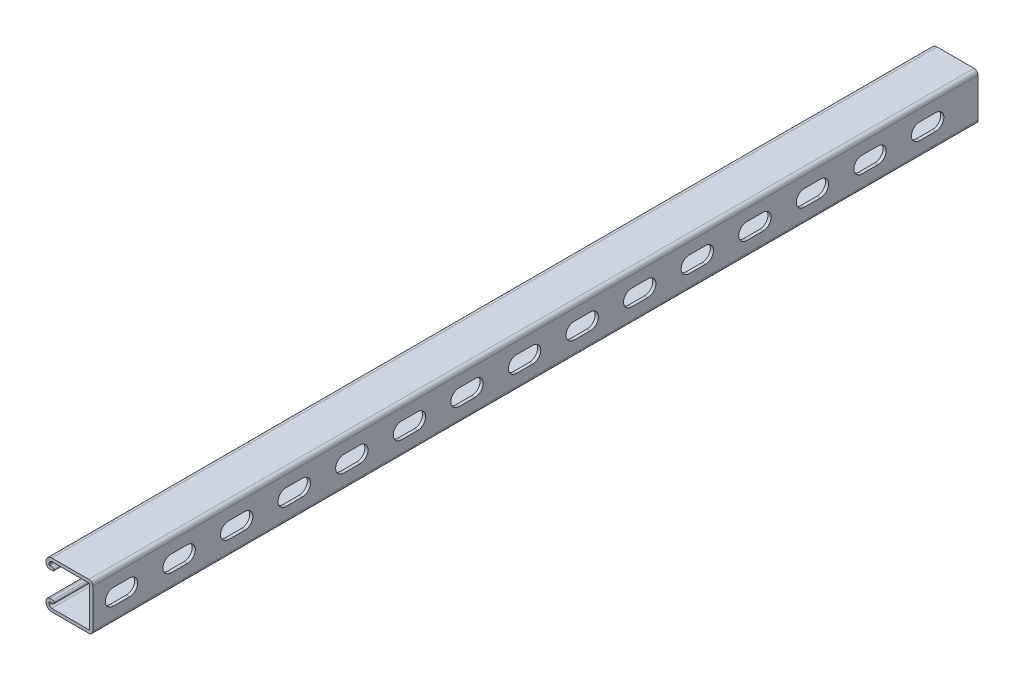
SolidWorks part; units mm, degrees
ref_plane "Front Plane" through (0, 0, 0) normal (0, 0, 1) x (1, 0, 0)
ref_plane "Top Plane" through (0, 0, 0) normal (0, 1, 0) x (1, 0, 0)
ref_plane "Right Plane" through (0, 0, 0) normal (1, 0, 0) x (0, 0, -1)
sketch "Sketch1" plane through (0, 0, 0) normal (0, 0, 1) x (1, 0, 0)
  line L0 (0, 0) -> (-41.275, 0) construction
  line L3 (-41.275, 20.6375) -> (0, 20.6375) construction
  line L4 (-41.275, 20.6375) -> (-41.275, -20.6375) construction
  line L5 (-41.275, -20.6375) -> (0, -20.6375) construction
  line L6 (0, 20.6375) -> (0, -20.6375) construction
  line L7 (-36.2267, 20.6375) -> (-3.4607, 20.6375)
  line L8 (0, 17.1767) -> (0, -17.1767)
  line L9 (-2.794, -17.1767) -> (-2.794, 17.1767)
  line L10 (-3.4608, 17.8435) -> (-36.2267, 17.8435)
  line L11 (-41.275, 15.5892) -> (-41.275, 14.5732)
  line L12 (-37.8142, 11.1125) -> (-35.5346, 11.1125)
  line L14 (-35.5346, 13.9065) -> (-37.8142, 13.9065)
  line L15 (-38.481, 14.5732) -> (-38.481, 15.5892)
  line L16 (-38.481, -14.5733) -> (-38.481, -15.5893)
  line L17 (-35.5346, -13.9065) -> (-37.8142, -13.9065)
  line L18 (-37.8142, -11.1125) -> (-35.5346, -11.1125)
  line L19 (-41.275, -15.5893) -> (-41.275, -14.5733)
  line L20 (-3.4607, -17.8435) -> (-36.2267, -17.8435)
  line L21 (-36.2267, -20.6375) -> (-3.4607, -20.6375)
  line L22 (-2.794, -20.6375) -> (-2.794, 20.6375) construction
  arc A1 (0, 17.1767) -> (-3.4607, 20.6375) centre (-3.4607, 17.1767) ccw
  arc A2 (-2.794, 17.1767) -> (-3.4608, 17.8435) centre (-3.4607, 17.1767) ccw
  arc A4 (-36.2267, 20.6375) -> (-41.275, 15.5892) centre (-36.2267, 15.5892) ccw
  arc A5 (-41.275, 14.5732) -> (-37.8142, 11.1125) centre (-37.8142, 14.5732) ccw
  arc A6 (-35.5346, 11.1125) -> (-35.5346, 13.9065) centre (-35.5346, 12.5095) ccw
  arc A7 (-37.8142, 13.9065) -> (-38.481, 14.5732) centre (-37.8142, 14.5732) cw
  arc A8 (-38.481, 15.5892) -> (-36.2267, 17.8435) centre (-36.2267, 15.5892) cw
  arc A9 (-38.481, -15.5893) -> (-36.2267, -17.8435) centre (-36.2267, -15.5893) ccw
  arc A10 (-37.8142, -13.9065) -> (-38.481, -14.5733) centre (-37.8142, -14.5733) ccw
  arc A11 (-35.5346, -11.1125) -> (-35.5346, -13.9065) centre (-35.5346, -12.5095) cw
  arc A12 (-41.275, -14.5733) -> (-37.8142, -11.1125) centre (-37.8142, -14.5733) cw
  arc A13 (-36.2267, -20.6375) -> (-41.275, -15.5893) centre (-36.2267, -15.5893) cw
  arc A14 (-2.794, -17.1767) -> (-3.4607, -17.8435) centre (-3.4607, -17.1767) cw
  arc A15 (0, -17.1767) -> (-3.4607, -20.6375) centre (-3.4607, -17.1767) cw
  point P24 (0, 20.6375)
  point P65 (-2.794, 0)
  dimension "D1" = 3.4608
  dimension "D2" = 5.0482
  dimension "D3" = 3.4608
  dimension "Ht." = 41.275
  dimension "Wd." = 41.275
  dimension "Thk." = 2.794
  dimension "D4" = 9.525
  dimension "D5" = 7.1374
extrude "Boss-Extrude1" add sketch "Sketch1" against normal blind 781.05
sketch "Sketch3" plane through (0, 0, 0) normal (1, 0, 0) x (0, 0, -1)
  line L0 (0, 0) -> (781.05, 0) construction
  point P2 (101.6, 0)
  point P3 (679.45, 0)
  dimension "D1" = 101.6
  dimension "D2" = 101.6
  dimension "D3" = 781.05
sketch "Sketch2" plane through (0, 0, 0) normal (1, 0, 0) x (0, 0, -1)
  line L0 (18.2562, 0) -> (32.5437, 0) construction
  line L1 (18.2562, 7.1437) -> (32.5437, 7.1437)
  line L2 (18.2562, -7.1437) -> (32.5437, -7.1437)
  line L3 (18.2562, 0) -> (0, 0) construction
  line L4 (25.4, 0) -> (76.2, 0) construction
  line L5 (0, -17.1767) -> (0, 17.1767) construction
  arc A0 (18.2562, 7.1437) -> (18.2562, -7.1437) centre (18.2562, 0) ccw
  arc A1 (32.5437, -7.1437) -> (32.5437, 7.1437) centre (32.5437, 0) ccw
  point P3 (25.4, 0)
  dimension "Hole to End" = 11.1125
  dimension "D2" = 25.4
extrude "Cut-Extrude1" cut sketch "Sketch2" against normal up to vertex (2.794 mm away) up to point (-2.794, 0, 0)
pattern_linear "LPattern1" count 15 spacing 50.8 along (0, 0, -1) of "Cut-Extrude1"
equation "\"D1@LPattern1\" = \"Slot Ctr.@Sketch2\""
equation "\"Hole Count@LPattern1\" = \"Lg.@Boss-Extrude1\" / \"D1@LPattern1\""
equation "\"D3@Sketch3\" = \"Lg.@Boss-Extrude1\""
